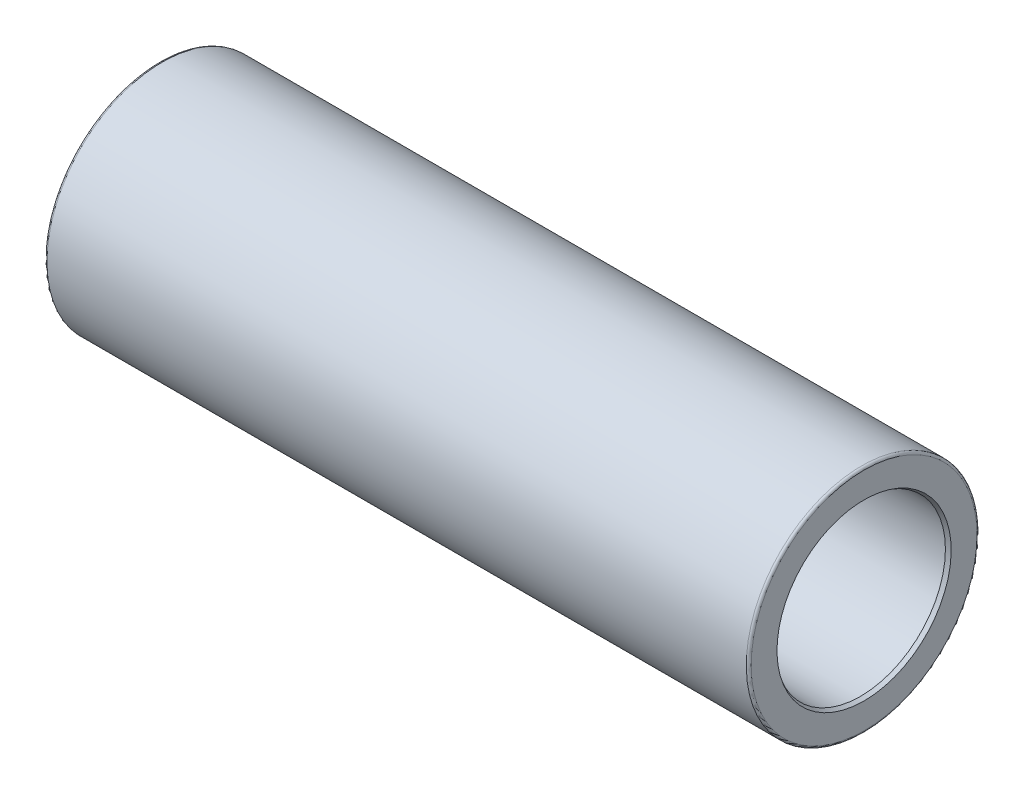
SolidWorks part; units mm, degrees
ref_plane "Plane1" through (0, 0, 0) normal (0, 0, 1) x (1, 0, 0)
ref_plane "Plane2" through (0, 0, 0) normal (0, 1, 0) x (1, 0, 0)
ref_plane "Plane3" through (0, 0, 0) normal (1, 0, 0) x (0, 0, -1)
sketch "Sketch1" plane through (0, 0, 0) normal (0, 0, 1) x (1, 0, 0)
  line L0 (-145, 0) -> (145, 0) construction
  line L1 (0, 93.3) -> (0, -101.2) construction
  line L2 (-145, 35) -> (-145, 46.5)
  line L3 (-144, 47.5) -> (144, 47.5)
  line L5 (-145, 35) -> (-65, 35)
  line L13 (145, 35) -> (65, 35)
  line L15 (145, 35) -> (145, 46.5)
  line L16 (-65, 35) -> (-58.297, 37.4397)
  line L17 (-57.955, 37.5) -> (57.955, 37.5)
  line L18 (65, 35) -> (58.297, 37.4397)
  arc A0 (-57.955, 37.5) -> (-58.297, 37.4397) centre (-57.955, 36.5) ccw
  arc A2 (57.955, 37.5) -> (58.297, 37.4397) centre (57.955, 36.5) cw
  arc A4 (-144, 47.5) -> (-145, 46.5) centre (-144, 46.5) ccw
  arc A5 (144, 47.5) -> (145, 46.5) centre (144, 46.5) cw
  point P23 (0, 47.5)
  point P26 (0, 37.5)
  point P28 (-58.1313, 37.5)
  point P34 (58.1313, 37.5)
  point P40 (-145, 47.5)
  point P43 (145, 47.5)
  dimension "D14" = 1
  dimension "D15" = 1
  dimension "D1" = 290
  dimension "D2" = 95
  dimension "D3" = 20
  dimension "D4" = 80
  dimension "D6" = 70
  dimension "D7" = 75
revolve "Base-Revolve" add sketch "Sketch1" angle 360 about L0
sketch "Sketch5" plane through (0, 0, 0) normal (0, 0, 1) x (1, 0, 0)
  line L0 (0, 0) -> (145, 0) construction
  line L1 (145, -46.5) -> (145, 46.5) construction
  line L2 (145, 35.866) -> (143.5, 35)
  line L4 (0, 0) -> (0, 47.5) construction
  line L5 (145, 35) -> (143.5, 35)
  line L6 (145, 35) -> (145, 35.866)
  line L7 (144, 47.5) -> (-144, 47.5) construction
  line L8 (-145, 35) -> (-145, 35.866)
  line L9 (-145, 35) -> (-143.5, 35)
  line L10 (-145, 35.866) -> (-143.5, 35)
  line L11 (145, 35) -> (65, 35) construction
  dimension "D1" = 30
  dimension "D2" = 1.5
revolve "2.5 x 30 gr reifning" cut sketch "Sketch5" angle 360 about L0
sketch "Sketch4" plane through (0, 0, 0) normal (1, 0, 0) x (0, 0, -1)
  line L1 (0, 0) -> (47.5, 0) construction
  line L2 (47.5, 0) -> (47.5, 10)
  line L3 (47.5, 10) -> (45.5, 10)
  line L4 (45.5, 10) -> (42.1352, 4.4)
  line L5 (42.1352, 4.4) -> (17.5, 4.4)
  line L6 (17.5, 4.4) -> (17.5, 0)
  line L7 (47.5, 0) -> (17.5, 0)
  line L8 (0, 0) -> (0, 47.5) construction
  circle A1 centre (0, 0) radius 47.5 construction
  circle A2 centre (0, 0) radius 47.5 construction
  dimension "D1" = 90
  dimension "D2" = 20
  dimension "D3" = 8.8
  dimension "D4" = 59
  dimension "D5" = 2
  dimension "D6" = 30
revolve "Udboring smørenippel" [suppressed] cut sketch "Sketch4" angle 360 about L1
cosmetic thread "Cosmetic Thread1" [suppressed] parameters "D2"=9.728
